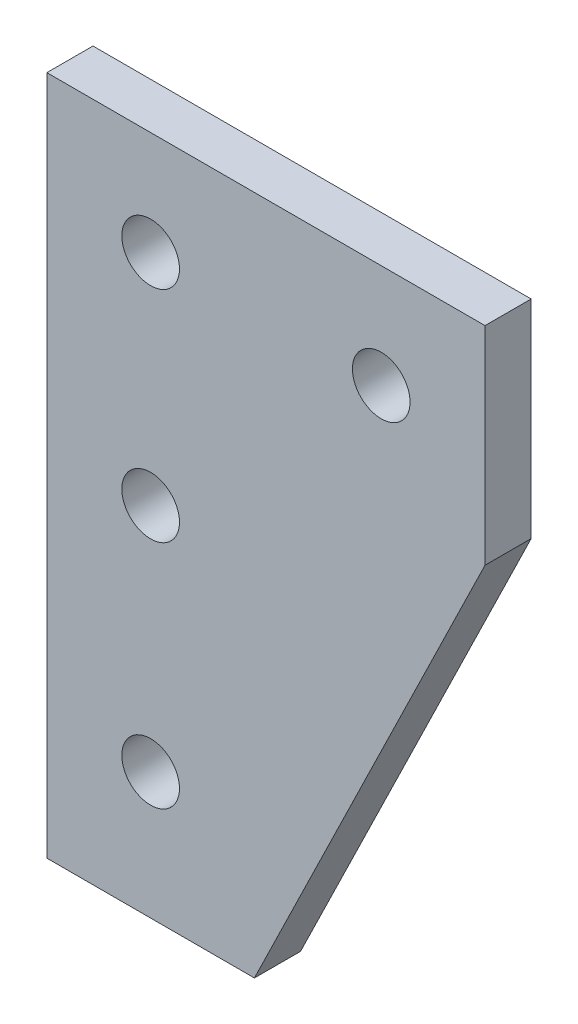
SolidWorks part; units mm, degrees
ref_plane "正面" through (0, 0, 0) normal (0, 0, 1) x (1, 0, 0)
ref_plane "平面" through (0, 0, 0) normal (0, 1, 0) x (1, 0, 0)
ref_plane "右側面" through (0, 0, 0) normal (1, 0, 0) x (0, 0, -1)
sketch "ｽｹｯﾁ1" plane through (0, 0, 0) normal (0, 0, 1) x (1, 0, 0)
  line L1 (-25, 25) -> (25, 25)
  line L2 (-25, 25) -> (-25, -25)
  line L3 (-25, -25) -> (25, -25)
  line L4 (25, 25) -> (25, -25)
  line L5 (-25, 25) -> (25, -25) construction
  line L6 (-25, -25) -> (25, 25) construction
  point P0 (0, 0)
  dimension "D1" = 50
  dimension "D2" = 50
extrude "ﾎﾞｽ - 押し出し1" add sketch "ｽｹｯﾁ1" along normal blind 2
sketch "ｽｹｯﾁ2" plane through (0, 0, 2) normal (0, 0, 1) x (1, 0, 0)
  line L0 (0, 0) -> (0, -9.51)
  line L1 (0, -9.51) -> (0, -19.51)
  line L2 (0, 0) -> (10, 0)
  circle A0 centre (0, 0) radius 1.6
  circle A1 centre (0, -9.51) radius 1.6
  circle A2 centre (0, -19.51) radius 1.6
  circle A3 centre (10, 0) radius 1.6
  dimension "D4" = 3.2
  dimension "D5" = 3.2
  dimension "D6" = 3.2
  dimension "D7" = 3.2
  dimension "D1" = 9.51
  dimension "D2" = 10
  dimension "D3" = 10
sketch "ｽｹｯﾁ3" plane through (0, 0, 2) normal (0, 0, 1) x (1, 0, 0)
  line L0 (14.5, -4.5) -> (4.5, -25)
  line L2 (-4.5, 4.5) -> (-4.5, -25)
  line L3 (-25, -25) -> (25, -25) construction
  line L4 (-39.2263, 35.2493) -> (37.3228, 35.2493)
  line L6 (4.5, -25) -> (-4.5, -25)
  line L7 (-39.2263, 35.2493) -> (-39.2263, -28.247)
  line L8 (-39.2263, -28.247) -> (37.3228, -28.247)
  line L9 (37.3228, 35.2493) -> (37.3228, -28.247)
  line L11 (-39.2263, 35.2493) -> (37.3228, -28.247) construction
  line L13 (-4.5, 4.5) -> (14.5, 4.5)
  line L14 (14.5, 4.5) -> (14.5, -4.5)
  line L15 (-39.2263, -28.247) -> (37.3228, 35.2493) construction
  point P0 (-0.9518, 3.5011)
extrude "ｶｯﾄ - 押し出し3" cut sketch "ｽｹｯﾁ3" against normal blind 10
hole_wizard "M3x0.5 ねじ穴1" positions "3Dｽｹｯﾁ1" profile "ｽｹｯﾁ4" tap size "M3x0.5" standard "JIS"
sketch3d "3Dｽｹｯﾁ1"
  point P0 (0, 0, 2)
  point P3 (10, 0, 2)
  point P6 (0, -9.51, 2)
  point P9 (0, -19.51, 2)
sketch "ｽｹｯﾁ4" plane through (0, 0, 2) normal (1, 0, 0) x (0, -1, 0)
  line L0 (0, 0) -> (0, 9.2511)
  line L1 (0, 9.2511) -> (1.25, 8.5)
  line L2 (1.25, 8.5) -> (1.25, 0)
  line L5 (1.25, 0) -> (0, 0)
  line L10 (0, 9.2511) -> (-1.25, 8.5) construction
  line L11 (0, -6.35) -> (0, 107.95) construction
  dimension "ねじ下穴ﾄﾞﾘﾙ直径" = 2.5
  dimension "ねじ下穴ﾄﾞﾘﾙの深さ" = 8.5
  dimension "ﾄﾞﾘﾙ角度" = 118
cosmetic thread "穴のねじ山1" parameters "D1"=2, "D2"=3
cosmetic thread "穴のねじ山2" parameters "D1"=2, "D2"=3
cosmetic thread "穴のねじ山3" parameters "D1"=2, "D2"=3
cosmetic thread "穴のねじ山4" parameters "D1"=2, "D2"=3
